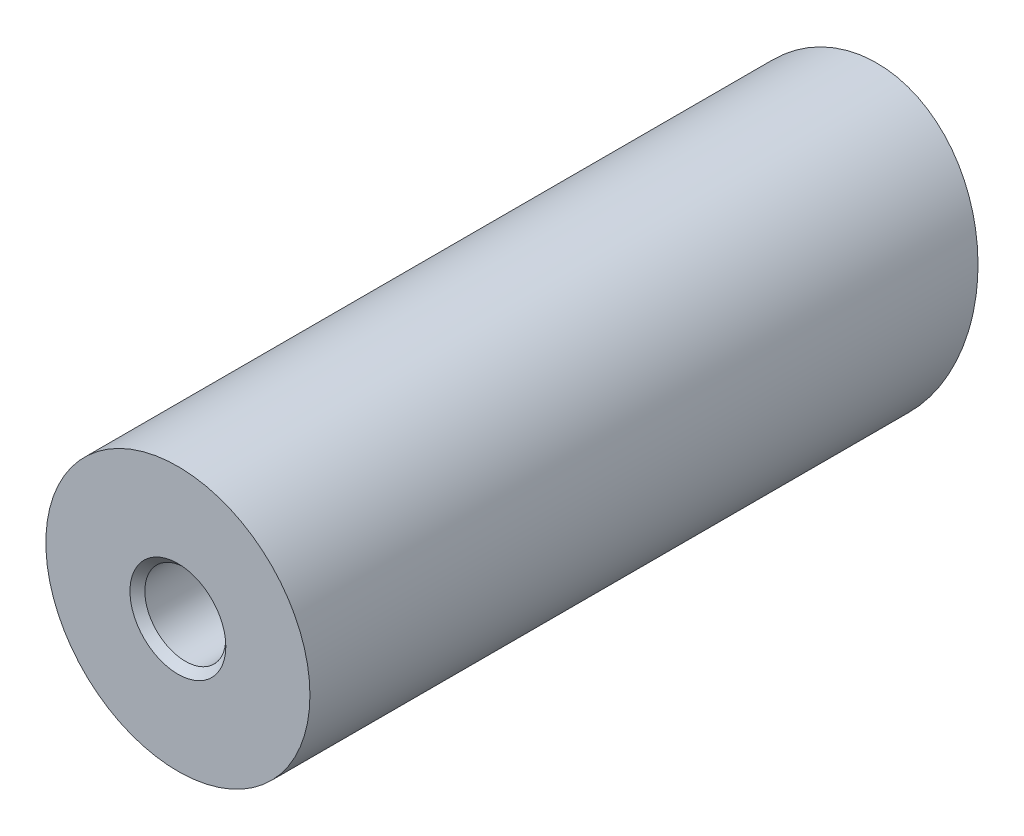
SolidWorks part; units mm, degrees
ref_plane "Ebene vorne" through (0, 0, 0) normal (0, 0, 1) x (1, 0, 0)
ref_plane "Ebene oben" through (0, 0, 0) normal (0, 1, 0) x (1, 0, 0)
ref_plane "Ebene rechts" through (0, 0, 0) normal (1, 0, 0) x (0, 0, -1)
sketch "Skizze1" plane through (0, 0, 0) normal (1, 0, 0) x (0, 0, -1)
  line L0 (0, 0) -> (78.253, 0) construction
  line L2 (0, 0) -> (58.6649, 0)
  line L3 (0, 0) -> (0, 11.0856)
  line L4 (0, 11.0856) -> (58.6649, 11.0856)
  line L5 (58.6649, 0) -> (58.6649, 11.0856)
revolve "Rotation1" add sketch "Skizze1" angle 360 about L0
sketch "Skizze2" plane through (0, 0, 0) normal (1, 0, 0) x (0, 0, -1)
  line L0 (58.6649, 11.0856) -> (52.7242, -11.0856)
  line L2 (58.6649, -11.0856) -> (58.6649, 11.0856) construction
  line L3 (0, -11.0856) -> (58.6649, -11.0856) construction
  line L4 (52.7242, -11.0856) -> (58.6649, -11.0856)
  line L5 (58.6649, 11.0856) -> (58.6649, -11.0856)
  dimension "D1" = 15
extrude "Schnitt-Linear austragen1" cut sketch "Skizze2" against normal mid plane 26
hole_wizard "M8 Gewindebohrung1" positions "Skizze4" profile "Skizze3" tap size "M8" standard "DIN"
sketch "Skizze4" plane through (0, 0, 0) normal (0, 0, 1) x (1, 0, 0)
  point P0 (0, 0)
sketch "Skizze3" plane through (0, 0, 0) normal (1, 0, 0) x (0, -1, 0)
  line L0 (0, 0) -> (0, 24.2929)
  line L1 (0, 24.2929) -> (3.4, 22.25)
  line L2 (3.4, 22.25) -> (3.4, 0.625)
  line L3 (3.4, 0.625) -> (4.025, 0)
  line L5 (4.025, 0) -> (0, 0)
  line L6 (-3.4, 0.625) -> (-4.025, 0) construction
  line L10 (0, 24.2929) -> (-3.4, 22.25) construction
  line L11 (0, -6.35) -> (0, 107.95) construction
  dimension "Bohrerdurchmesser" = 6.8
  dimension "Bohrungstiefe" = 22.25
  dimension "Senkdurchmesser (Oben)" = 8.05
  dimension "Senkwinkel (Oben)" = 90
  dimension "Spitzenwinkel" = 118
cosmetic thread "Bohrungsgewinde1" parameters "D1"=18.0593, "D2"=8
sketch "Skizze5" plane through (0, -13.9236, -51.9637) normal (0, -0.2588, -0.9659) x (-1, 0, 0)
  ellipse E0 centre (0, 14.4148) end of major axis (0, 2.9382) minor radius 11.0856 construction
  point P0 (0, 25.8915)
ref_plane "Ebene1" through (0, 0, -58.6649) normal (0, 0, 1) x (1, 0, 0)
hole_wizard "M8 Gewindebohrung2" positions "Skizze7" profile "Skizze6" tap size "M8" standard "DIN"
sketch "Skizze7" plane through (0, 0, -58.6649) normal (0, 0, 1) x (1, 0, 0)
  point P0 (0, 0)
sketch "Skizze6" plane through (0, 0, -58.6649) normal (1, 0, 0) x (0, 1, 0)
  line L0 (0, 0) -> (0, 24.2929)
  line L1 (0, 24.2929) -> (3.4, 22.25)
  line L2 (3.4, 22.25) -> (3.4, 0.625)
  line L3 (3.4, 0.625) -> (4.025, 0)
  line L5 (4.025, 0) -> (0, 0)
  line L6 (-3.4, 0.625) -> (-4.025, 0) construction
  line L10 (0, 24.2929) -> (-3.4, 22.25) construction
  line L11 (0, -6.35) -> (0, 107.95) construction
  dimension "Bohrerdurchmesser" = 6.8
  dimension "Bohrungstiefe" = 22.25
  dimension "Senkdurchmesser (Oben)" = 8.05
  dimension "Senkwinkel (Oben)" = 90
  dimension "Spitzenwinkel" = 118
cosmetic thread "Bohrungsgewinde2" parameters "D1"=16, "D2"=8
